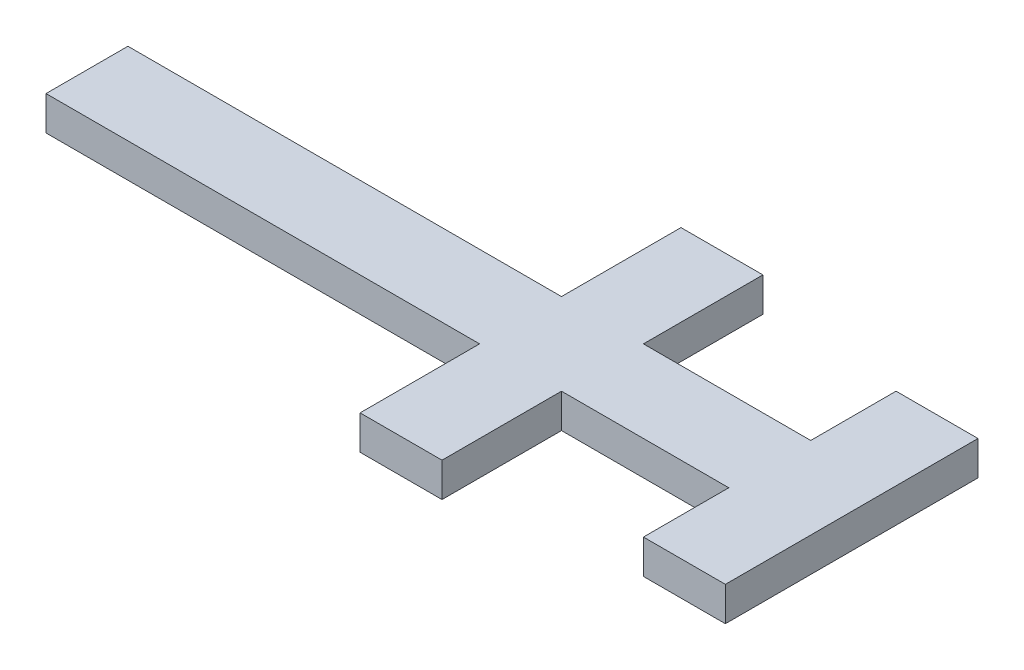
SolidWorks part; units mm, degrees
ref_plane "前视基准面" through (0, 0, 0) normal (0, 0, 1) x (1, 0, 0)
ref_plane "上视基准面" through (0, 0, 0) normal (0, 1, 0) x (1, 0, 0)
ref_plane "右视基准面" through (0, 0, 0) normal (1, 0, 0) x (0, 0, -1)
other "Configuration Table"
sketch "草图2" plane through (0, 0, 0) normal (0, 1, 0) x (1, 0, 0)
  line L0 (0, 0) -> (-41, 0) construction
  line L5 (-14, -5) -> (14, -5)
  line L6 (-14, -5) -> (-14, 5)
  line L7 (-14, 5) -> (14, 5)
  line L8 (14, -5) -> (14, 5)
  line L9 (-14, -5) -> (14, 5) construction
  line L10 (-14, 5) -> (14, -5) construction
  line L11 (19, 0) -> (14, 0) construction
  line L12 (-21, -5) -> (-61, -5)
  line L13 (-21, -5) -> (-21, 5)
  line L14 (-21, 5) -> (-61, 5)
  line L15 (-61, -5) -> (-61, 5)
  line L16 (-21, -5) -> (-61, 5) construction
  line L17 (-21, 5) -> (-61, -5) construction
  line L18 (-12.5, -22.5) -> (-22.5, -22.5)
  line L19 (-12.5, -22.5) -> (-12.5, 22.5)
  line L20 (-12.5, 22.5) -> (-22.5, 22.5)
  line L21 (-22.5, -22.5) -> (-22.5, 22.5)
  line L22 (-12.5, -22.5) -> (-22.5, 22.5) construction
  line L23 (-12.5, 22.5) -> (-22.5, -22.5) construction
  line L24 (24, -17.5) -> (14, -17.5)
  line L25 (24, -17.5) -> (24, 17.5)
  line L26 (24, 17.5) -> (14, 17.5)
  line L27 (14, -17.5) -> (14, 17.5)
  line L28 (24, -17.5) -> (14, 17.5) construction
  line L29 (24, 17.5) -> (14, -17.5) construction
  line L31 (-61, 5) -> (-86, 5)
  line L32 (-61, 5) -> (-61, -5)
  line L33 (-61, -5) -> (-86, -5)
  line L34 (-86, 5) -> (-86, -5)
  point P0 (0, 0)
  point P13 (19, 0)
  point P15 (-17.5, 0)
  dimension "D1" = 10
  dimension "D2" = 28
  dimension "D3" = 40
  dimension "D4" = 10
  dimension "D5" = 41
  dimension "D6" = 10
  dimension "D7" = 3.5
  dimension "D8" = 45
  dimension "D9" = 10
  dimension "D10" = 5
  dimension "D11" = 35
  dimension "D12" = 25
sketch "草图3" plane through (0, 0, 0) normal (0, 1, 0) x (1, 0, 0)
  line L0 (-14, -5) -> (14, -5) construction
  line L1 (24, 17.5) -> (14, 17.5)
  line L2 (24, 17.5) -> (24, -17.5)
  line L3 (24, -17.5) -> (14, -17.5)
  line L4 (14, 17.5) -> (14, -17.5)
  line L5 (14, 5) -> (-12.5, 5)
  line L6 (14, 5) -> (14, -5)
  line L7 (14, -5) -> (-12.5, -5)
  line L8 (-12.5, 5) -> (-12.5, -5)
  line L9 (-12.5, -22.5) -> (-12.5, 22.5) construction
  line L10 (-21, 5) -> (-61, 5) construction
  line L11 (-12.5, 22.5) -> (-22.5, 22.5)
  line L12 (-12.5, 22.5) -> (-12.5, -22.5)
  line L13 (-12.5, -22.5) -> (-22.5, -22.5)
  line L14 (-22.5, 22.5) -> (-22.5, -22.5)
  line L15 (-61, -5) -> (-22.5, -5)
  line L16 (-61, -5) -> (-61, 5)
  line L17 (-61, 5) -> (-22.5, 5)
  line L18 (-22.5, -5) -> (-22.5, 5)
  line L20 (-61, 5) -> (-86, 5)
  line L21 (-61, 5) -> (-61, -5)
  line L22 (-61, -5) -> (-86, -5)
  line L23 (-86, 5) -> (-86, -5)
extrude "凸台-拉伸1" add sketch "草图3" along normal blind 1 contours L1 L4 L3 L2 | L5 L8 L7 L4 | L11 L14 L13 L12 L8 | L17 L16 L15 L14 | L20 L23 L22 L16
sketch "草图4" plane through (0, 0, 0) normal (0, -1, 0) x (1, 0, 0)
  line L0 (13, -18.5) -> (25, -18.5)
  line L1 (25, -18.5) -> (25, 18.5)
  line L2 (25, 18.5) -> (13, 18.5)
  line L3 (13, 18.5) -> (13, 6)
  line L4 (13, 6) -> (-11.5, 6)
  line L5 (-11.5, 6) -> (-11.5, 23.5)
  line L6 (-11.5, 23.5) -> (-23.5, 23.5)
  line L7 (-23.5, 23.5) -> (-23.5, 6)
  line L8 (-23.5, 6) -> (-87, 6)
  line L9 (-87, 6) -> (-87, -6)
  line L10 (-87, -6) -> (-23.5, -6)
  line L11 (-23.5, -6) -> (-23.5, -23.5)
  line L12 (-23.5, -23.5) -> (-11.5, -23.5)
  line L13 (-11.5, -23.5) -> (-11.5, -6)
  line L14 (-11.5, -6) -> (13, -6)
  line L15 (13, -6) -> (13, -18.5)
  line L16 (14, -17.5) -> (24, -17.5)
  line L17 (24, -17.5) -> (24, 17.5)
  line L18 (24, 17.5) -> (14, 17.5)
  line L19 (14, 17.5) -> (14, 5)
  line L20 (14, 5) -> (-12.5, 5)
  line L21 (-12.5, 5) -> (-12.5, 22.5)
  line L22 (-12.5, 22.5) -> (-22.5, 22.5)
  line L23 (-22.5, 22.5) -> (-22.5, 5)
  line L24 (-22.5, 5) -> (-86, 5)
  line L25 (-86, 5) -> (-86, -5)
  line L26 (-86, -5) -> (-22.5, -5)
  line L27 (-22.5, -5) -> (-22.5, -22.5)
  line L28 (-22.5, -22.5) -> (-12.5, -22.5)
  line L29 (-12.5, -22.5) -> (-12.5, -5)
  line L30 (-12.5, -5) -> (14, -5)
  line L31 (14, -5) -> (14, -17.5)
  line L32 (14, -17.5) -> (24, -17.5)
  line L33 (24, -17.5) -> (24, 17.5)
  line L34 (24, 17.5) -> (14, 17.5)
  line L35 (14, 17.5) -> (14, 5)
  line L36 (14, 5) -> (-12.5, 5)
  line L37 (-12.5, 5) -> (-12.5, 22.5)
  line L38 (-12.5, 22.5) -> (-22.5, 22.5)
  line L39 (-22.5, 22.5) -> (-22.5, 5)
  line L40 (-22.5, 5) -> (-86, 5)
  line L41 (-86, 5) -> (-86, -5)
  line L42 (-86, -5) -> (-22.5, -5)
  line L43 (-22.5, -5) -> (-22.5, -22.5)
  line L44 (-22.5, -22.5) -> (-12.5, -22.5)
  line L45 (-12.5, -22.5) -> (-12.5, -5)
  line L46 (-12.5, -5) -> (14, -5)
  line L47 (14, -5) -> (14, -17.5)
  dimension "D1" = 0
  dimension "D2" = 1
extrude "凸台-拉伸2" add sketch "草图4" along normal blind 4 and the other way blind 1
sketch "草图5" plane through (0, 0, 0) normal (0, -1, 0) x (1, 0, 0)
  line L0 (-22.5, 22.5) -> (-22.5, 5)
  line L1 (-86, 5) -> (-61, 5)
  line L2 (-86, 5) -> (-86, -5)
  line L3 (-86, -5) -> (-61, -5)
  line L4 (-61, 5) -> (-61, -5)
  line L5 (14, 17.5) -> (24, 17.5)
  line L6 (14, 17.5) -> (14, -17.5)
  line L7 (14, -17.5) -> (24, -17.5)
  line L8 (24, 17.5) -> (24, -17.5)
  line L9 (-22.5, 5) -> (-21, 5)
  line L10 (-21, 5) -> (-21, -5)
  line L11 (-21, -5) -> (-22.5, -5)
  line L12 (-22.5, -5) -> (-22.5, -22.5)
  line L13 (-22.5, -22.5) -> (-12.5, -22.5)
  line L14 (-12.5, -22.5) -> (-12.5, -5)
  line L15 (-12.5, -5) -> (-14, -5)
  line L16 (-14, -5) -> (-14, 5)
  line L17 (-14, 5) -> (-12.5, 5)
  line L18 (-12.5, 5) -> (-12.5, 22.5)
  line L19 (-12.5, 22.5) -> (-22.5, 22.5)
extrude "凸台-拉伸3" add sketch "草图5" along normal blind 2
